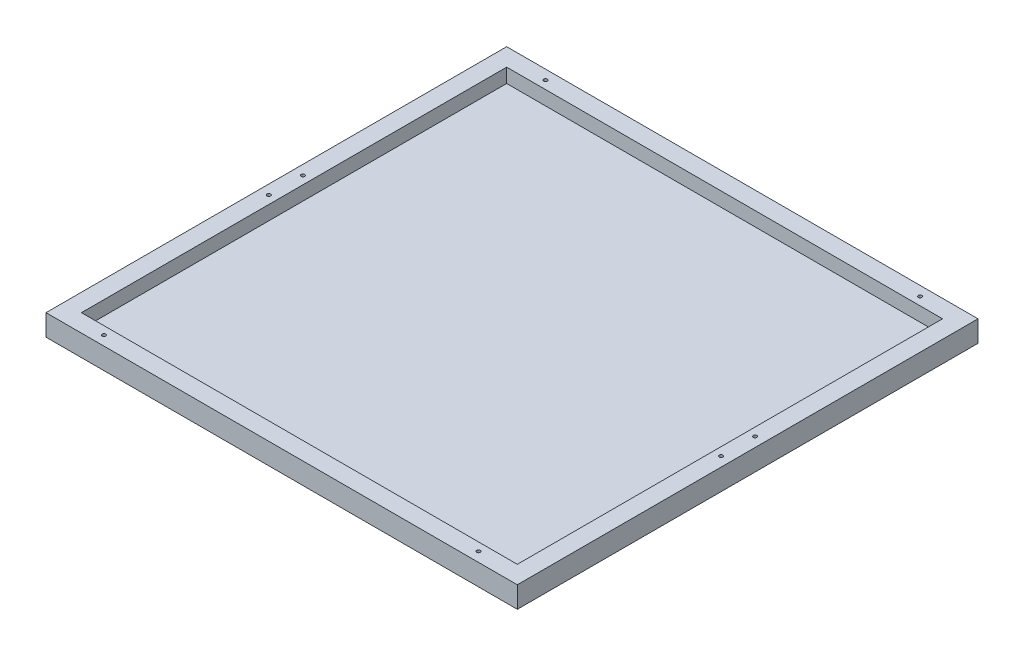
SolidWorks part; units mm, degrees
ref_plane "Front" through (0, 0, 0) normal (0, 0, 1) x (1, 0, 0)
ref_plane "Top" through (0, 0, 0) normal (0, 1, 0) x (1, 0, 0)
ref_plane "Right" through (0, 0, 0) normal (1, 0, 0) x (0, 0, -1)
sketch "Sketch1" plane through (0, 0, 0) normal (0, 1, 0) x (1, 0, 0)
  line L1 (0, 0) -> (665, 0)
  line L2 (0, 0) -> (0, 650)
  line L3 (0, 650) -> (665, 650)
  line L4 (665, 0) -> (665, 650)
  dimension "D1" = 665
  dimension "D2" = 650
extrude "Boss-Extrude1" add sketch "Sketch1" against normal blind 30
hole_wizard "#8 (0.199) Diameter Hole1" positions "Sketch3" profile "Sketch2" hole size "#8" standard "ANSI Inch"
sketch "Sketch3" plane through (0, 0, 0) normal (0, 1, 0) x (1, 0, 0)
  line L0 (0, 650) -> (0, 0) construction
  line L1 (0, 0) -> (665, 0) construction
  line L3 (332.5, 650) -> (332.5, 0) construction
  line L4 (665, 650) -> (0, 650) construction
  line L6 (0, 325) -> (665, 325) construction
  line L7 (665, 0) -> (665, 650) construction
  point P10 (68.25, 13.5)
  point P12 (13.5, 301)
  point P43 (596.75, 13.5)
  point P44 (651.5, 301)
  point P47 (651.5, 349)
  point P48 (596.75, 636.5)
  point P49 (68.25, 636.5)
  point P50 (13.5, 349)
  dimension "D1" = 13.5
  dimension "D4" = 301
  dimension "D5" = 13.5
  dimension "D6" = 68.25
sketch "Sketch2" plane through (68.25, 0, -13.5) normal (1, 0, 0) x (0, 0, 1)
  line L0 (0, 0) -> (0, 9.65)
  line L1 (0, 9.65) -> (2.5273, 9.65)
  line L2 (2.5273, 9.65) -> (2.5273, 0)
  line L5 (2.5273, 0) -> (0, 0)
  line L10 (0, 9.65) -> (-2.5273, 9.65) construction
  line L11 (0, -6.35) -> (0, 107.95) construction
  dimension "Hole Dia." = 5.0546
  dimension "Hole Depth" = 9.65
  dimension "Drill Angle" = 180
sketch "Sketch4" plane through (0, 0, 0) normal (0, 1, 0) x (1, 0, 0)
  line L0 (0, 650) -> (0, 0) construction
  line L1 (25, 625) -> (640, 625)
  line L2 (25, 625) -> (25, 25)
  line L3 (25, 25) -> (640, 25)
  line L4 (640, 625) -> (640, 25)
  line L5 (665, 650) -> (0, 650) construction
  line L6 (665, 0) -> (665, 650) construction
  line L7 (0, 0) -> (665, 0) construction
  dimension "D1" = 25
  dimension "D2" = 25
  dimension "D3" = 25
  dimension "D4" = 25
extrude "Cut-Extrude1" cut sketch "Sketch4" against normal blind 20
